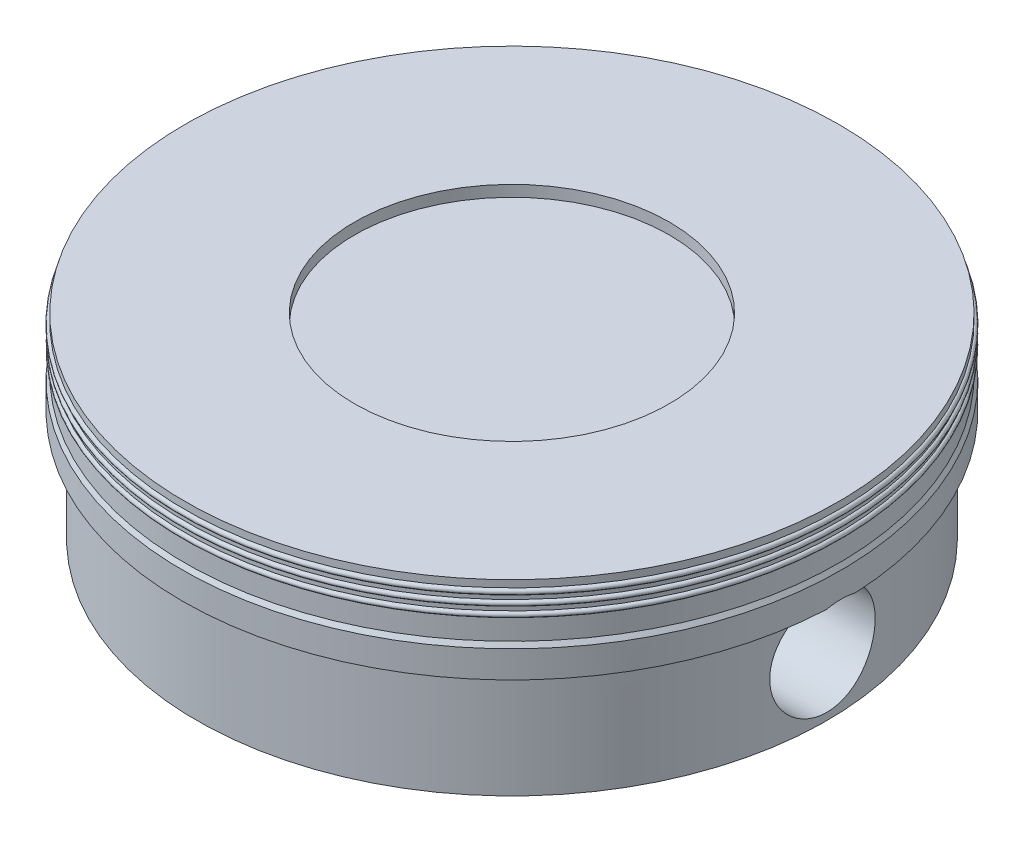
SolidWorks part; units mm, degrees
ref_plane "Front Plane" through (0, 0, 0) normal (0, 0, 1) x (1, 0, 0)
ref_plane "Top Plane" through (0, 0, 0) normal (0, 1, 0) x (1, 0, 0)
ref_plane "Right Plane" through (0, 0, 0) normal (1, 0, 0) x (0, 0, -1)
sketch "Sketch2" plane through (0, 0, 0) normal (0, 0, 1) x (1, 0, 0)
  line L0 (0, 0) -> (0, 3) construction
  line L1 (0, 0) -> (5, 0) construction
  line L2 (4.78, 0) -> (3.43, 0)
  line L3 (3.43, 0) -> (3.43, 1.93)
  line L4 (3.43, 1.93) -> (4.2, 1.93)
  line L5 (4.2, 1.93) -> (4.2, 2.33)
  line L6 (4.2, 2.33) -> (0, 2.33)
  line L7 (0, 2.33) -> (0, 2.8)
  line L8 (0, 2.8) -> (2.39, 2.8)
  line L9 (2.39, 2.8) -> (2.39, 2.97)
  line L10 (2.39, 2.97) -> (4.96, 2.97)
  line L11 (4.96, 2.97) -> (4.96, 2.8623)
  line L12 (4.96, 2.16) -> (5, 2.09)
  line L13 (5, 2.09) -> (5, 1.68)
  line L14 (5, 1.68) -> (4.78, 1.68)
  line L15 (4.78, 1.68) -> (4.78, 0)
  line L16 (4.96, 2.7777) -> (4.96, 2.71)
  line L17 (4.96, 2.63) -> (4.96, 2.56)
  line L18 (4.96, 2.48) -> (4.96, 2.16)
  arc A0 (4.96, 2.63) -> (4.96, 2.71) centre (4.96, 2.67) ccw
  arc A1 (4.96, 2.48) -> (4.96, 2.56) centre (4.96, 2.52) ccw
  arc A2 (4.96, 2.7777) -> (4.96, 2.8623) centre (4.96, 2.82) ccw
  point P23 (4.96, 2.1431)
  dimension "D14" = 0.15
  dimension "D1" = 3
  dimension "D2" = 5
  dimension "D3" = 4.96
  dimension "D4" = 0.04
  dimension "D5" = 1.68
  dimension "D6" = 0.22
  dimension "D7" = 1.35
  dimension "D8" = 1.93
  dimension "D9" = 0.4
  dimension "D10" = 2.57
  dimension "D11" = 0.17
  dimension "D12" = 0.47
  dimension "D13" = 4.2
  dimension "D15" = 0.15
  dimension "D16" = 0.15
  dimension "D17" = 0.41
  dimension "D18" = 0.07
revolve "Revolve1" add sketch "Sketch2" angle 360 about L0
sketch "Sketch4" plane through (0, 2.33, 0) normal (0, -1, 0) x (1, 0, 0)
  line L0 (0, 0) -> (0, 3.43) construction
  line L1 (0, 0) -> (-3.43, 0) construction
  line L2 (-1.5, 3.0846) -> (-1.5, -3.0846)
  line L3 (1.5, 3.0846) -> (1.5, -3.0846)
  circle A0 centre (0, 0) radius 3.43 construction
  arc A1 (-1.5, 3.0846) -> (-1.5, -3.0846) centre (0, 0) ccw
  arc A2 (1.5, -3.0846) -> (1.5, 3.0846) centre (0, 0) ccw
  point P9 (0, 0)
  dimension "D1" = 3
extrude "Boss-Extrude2" add sketch "Sketch4" along normal up to surface (2.33 mm away) up to face at (0, 0, -4.78)
sketch "Sketch5" plane through (0, 0, 0) normal (1, 0, 0) x (0, 0, -1)
  circle A0 centre (0, 0.91) radius 0.8
  dimension "D1" = 1.6
  dimension "D2" = 0.91
extrude "Cut-Extrude1" cut sketch "Sketch5" against normal through all both and the other way through all
